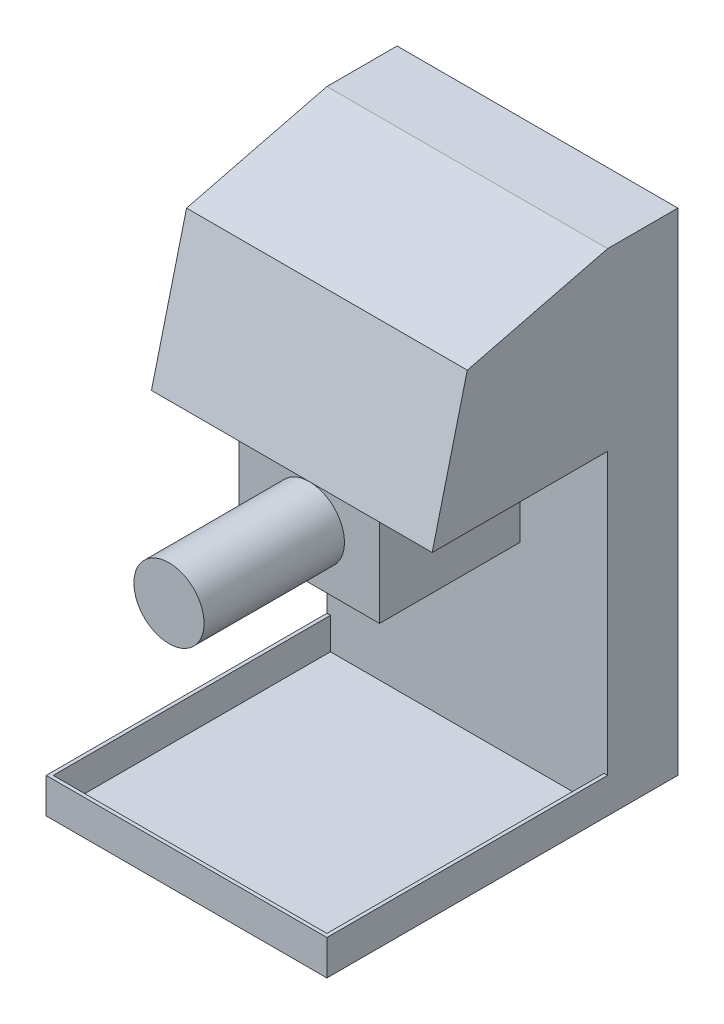
SolidWorks part; units mm, degrees
ref_plane "Front Plane" through (0, 0, 0) normal (0, 0, 1) x (1, 0, 0)
ref_plane "Top Plane" through (0, 0, 0) normal (0, 1, 0) x (1, 0, 0)
ref_plane "Right Plane" through (0, 0, 0) normal (1, 0, 0) x (0, 0, -1)
sketch "Sketch1" plane through (0, 0, 0) normal (1, 0, 0) x (0, 0, -1)
  line L0 (0, 0) -> (0, 140)
  line L1 (0, 140) -> (-20, 140)
  line L2 (-20, 140) -> (-60, 130)
  line L3 (-60, 130) -> (-70, 90)
  line L4 (-70, 90) -> (-20, 90)
  line L5 (-20, 90) -> (-20, 10)
  line L6 (-20, 10) -> (-100, 10)
  line L7 (-100, 10) -> (-100, 0)
  line L8 (-100, 0) -> (0, 0)
  point P12 (-55.8846, 139.4551)
  dimension "D1" = 140
  dimension "D2" = 100
  dimension "D3" = 10
  dimension "D4" = 20
  dimension "D5" = 20
  dimension "D6" = 40
  dimension "D7" = 10
  dimension "D8" = 40
  dimension "D9" = 10
extrude "Boss-Extrude1" add sketch "Sketch1" along normal blind 80
sketch "Sketch2" plane through (0, 90, 0) normal (0, -1, 0) x (1, 0, 0)
  line L0 (80, 70) -> (80, 20) construction
  line L1 (60, 65) -> (20, 65)
  line L2 (60, 65) -> (60, 25)
  line L3 (60, 25) -> (20, 25)
  line L4 (20, 65) -> (20, 25)
  line L5 (80, 45) -> (0, 45) construction
  line L6 (0, 70) -> (0, 20) construction
  line L7 (40, 70) -> (40, 20) construction
  line L8 (80, 70) -> (0, 70) construction
  line L9 (80, 20) -> (0, 20) construction
  point P6 (60, 45)
  point P18 (40, 65)
  dimension "D1" = 40
extrude "Boss-Extrude2" add sketch "Sketch2" along normal blind 30
sketch "Sketch3" plane through (0, 0, 65) normal (0, 0, 1) x (1, 0, 0)
  line L0 (20, 60) -> (20, 90) construction
  line L2 (60, 60) -> (20, 60) construction
  circle A0 centre (40, 75) radius 10
  dimension "D1" = 20
  dimension "D2" = 20
  dimension "D3" = 15
extrude "Boss-Extrude3" add sketch "Sketch3" along normal blind 40
sketch "Sketch4" plane through (0, 10, 0) normal (0, 1, 0) x (1, 0, 0)
  line L0 (80, -20) -> (0, -20) construction
  line L1 (79, -20) -> (1, -20)
  line L2 (79, -20) -> (79, -99)
  line L3 (79, -99) -> (1, -99)
  line L4 (1, -20) -> (1, -99)
  line L5 (80, -20) -> (80, -100) construction
  line L6 (80, -100) -> (0, -100) construction
  line L7 (0, -20) -> (0, -100) construction
  dimension "D1" = 1
  dimension "D2" = 1
  dimension "D3" = 1
extrude "Cut-Extrude1" cut sketch "Sketch4" against normal offset from surface (9 mm away) 1 up to face at (40, 0, 50)
